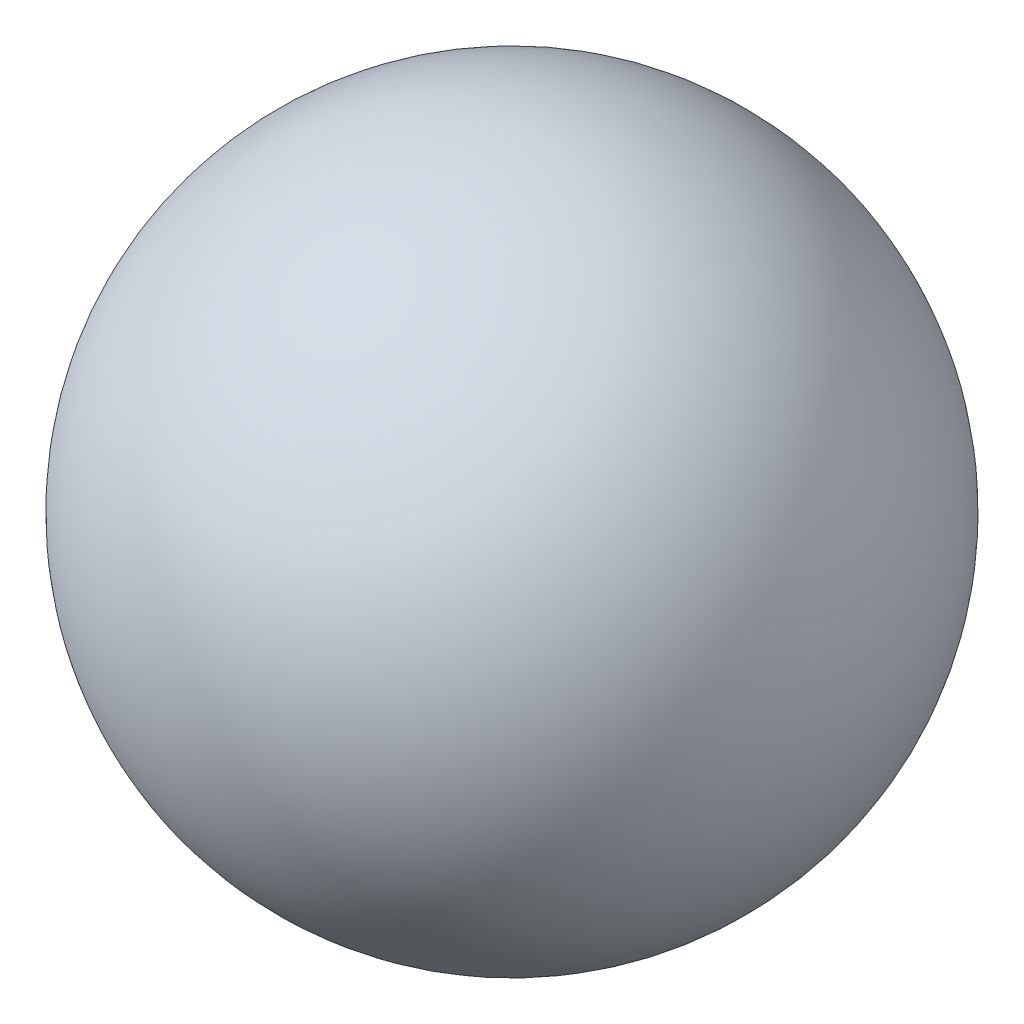
SolidWorks part; units mm, degrees
ref_plane "Front Plane" through (0, 0, 0) normal (0, 0, 1) x (1, 0, 0)
ref_plane "Top Plane" through (0, 0, 0) normal (0, 1, 0) x (1, 0, 0)
ref_plane "Right Plane" through (0, 0, 0) normal (1, 0, 0) x (0, 0, -1)
sketch "Sketch3" plane through (0, 0, 0) normal (0, 1, 0) x (1, 0, 0)
  line L0 (0, 20) -> (0, -20)
  arc A0 (0, 20) -> (0, -20) centre (0, 0) ccw
  dimension "D1" = 40
revolve "Revolve1" add sketch "Sketch3" angle 360 about L0
equation "\"0..00deg\"=1"
